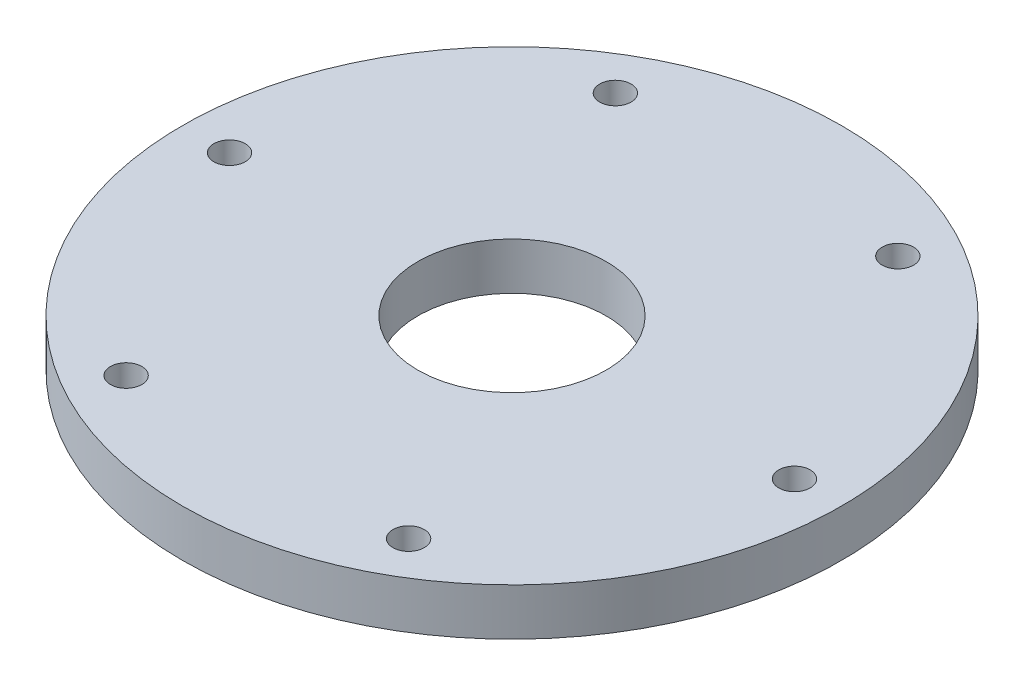
SolidWorks part; units mm, degrees
material "6061-T6 (SS)"
ref_plane "Front Plane" through (0, 0, 0) normal (0, 0, 1) x (1, 0, 0)
ref_plane "Top Plane" through (0, 0, 0) normal (0, 1, 0) x (1, 0, 0)
ref_plane "Right Plane" through (0, 0, 0) normal (1, 0, 0) x (0, 0, -1)
ref_axis "Axis1" through (0, -0.4763, 0) along (0, 1, 0)
sketch "Sketch1" plane through (0, 0, 0) normal (0, 1, 0) x (1, 0, 0)
  circle A0 centre (0, 0) radius 66.675
  circle A1 centre (0, 0) radius 19.05
  dimension "D1" = 133.35
  dimension "D2" = 38.1
extrude "Boss-Extrude1" add sketch "Sketch1" along normal blind 9.525
sketch "Sketch2" plane through (0, 0, 0) normal (0, 0, 1) x (1, 0, 0)
  line L1 (41.275, 0) -> (44.45, 0)
  line L2 (41.275, 0) -> (41.275, 3.81)
  line L3 (41.275, 3.81) -> (44.45, 3.81)
  line L4 (44.45, 0) -> (44.45, 3.81)
  line L6 (73.3425, 0) -> (-73.3425, 0) construction
  point P6 (0, 0)
  point P7 (0, 0)
  dimension "D1" = 3.81
  dimension "D2" = 3.175
  dimension "D3" = 44.45
revolve "Cut-Revolve1" cut sketch "Sketch2" angle 360 about axis through (0, -0.4763, 0) along (0, 1, 0)
hole_wizard "1/4 (0.25) Diameter Hole1" positions "Sketch5" profile "Sketch4" hole size "1/4" standard "ANSI Inch" end condition up to next
sketch "Sketch5" plane through (0, 9.525, 0) normal (0, 1, 0) x (1, 0, 0)
  line L0 (-5.2388, 0) -> (5.2388, 0) construction
  point P0 (57.15, 0)
  dimension "D1" = 57.15
sketch "Sketch4" plane through (57.15, 9.525, 0) normal (1, 0, 0) x (0, 0, 1)
  line L0 (0, 0) -> (0, 9.526)
  line L1 (0, 9.526) -> (3.175, 9.526)
  line L2 (3.175, 9.526) -> (3.175, 0)
  line L5 (3.175, 0) -> (0, 0)
  line L11 (0, -6.35) -> (0, 107.95) construction
  dimension "Thru Hole Dia." = 6.35
  dimension "Thru Hole Depth" = 9.526
pattern_circular "CirPattern1" count 6 over 360 about axis through (0, 0, 0) along (0, 1, 0) of "1/4 (0.25) Diameter Hole1"
